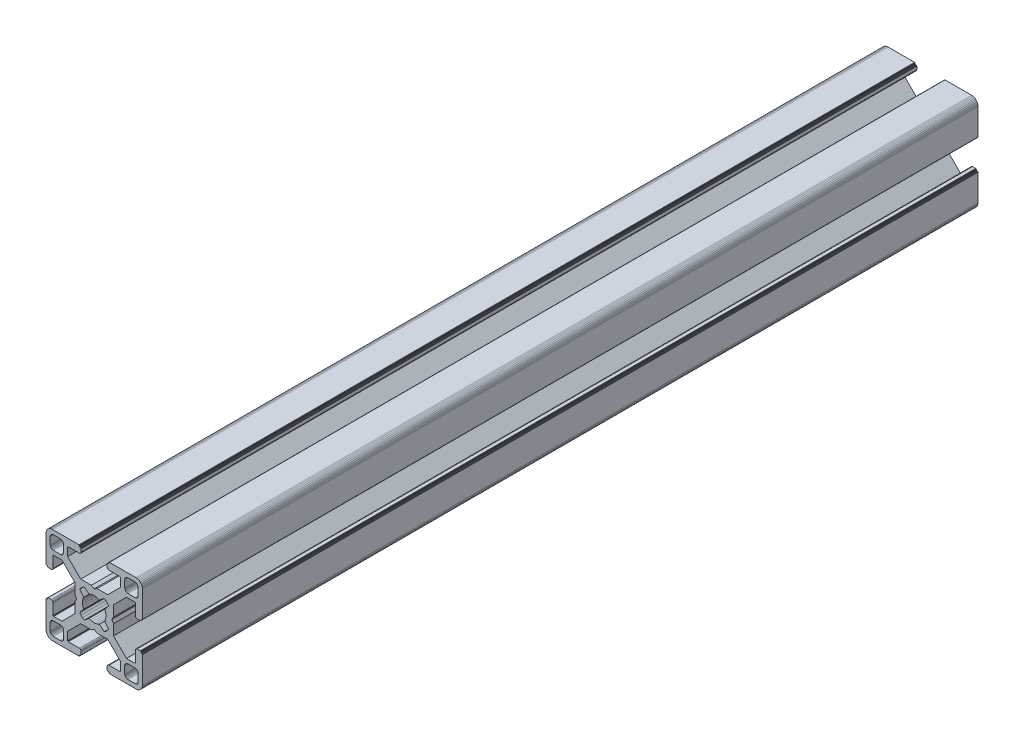
SolidWorks part; units mm, degrees
ref_plane "Front Plane" through (0, 0, 0) normal (0, 0, 1) x (1, 0, 0)
ref_plane "Top Plane" through (0, 0, 0) normal (0, 1, 0) x (1, 0, 0)
ref_plane "Right Plane" through (0, 0, 0) normal (1, 0, 0) x (0, 0, -1)
ref_plane "Plane1" through (0, 0, 0) normal (0, 0, 1) x (1, 0, 0)
sketch "Sketch1" plane through (0, 0, 0) normal (0, 0, 1) x (1, 0, 0)
  line L0 (28.3473, 29.9696) -> (28, 30)
  line L1 (28, 30) -> (19.75, 30)
  line L2 (19.75, 30) -> (19.7153, 29.997)
  line L3 (19.7153, 29.997) -> (19.6816, 29.9879)
  line L4 (19.6816, 29.9879) -> (19.65, 29.9732)
  line L5 (19.65, 29.9732) -> (19.6214, 29.9532)
  line L6 (19.6214, 29.9532) -> (19.5968, 29.9286)
  line L7 (19.5968, 29.9286) -> (19.5768, 29.9)
  line L8 (19.5768, 29.9) -> (19.5621, 29.8684)
  line L9 (19.5621, 29.8684) -> (19.553, 29.8347)
  line L10 (19.553, 29.8347) -> (19.55, 29.8)
  line L11 (19.55, 29.8) -> (19.55, 29.7)
  line L12 (19.55, 29.7) -> (19.547, 29.6653)
  line L13 (19.547, 29.6653) -> (19.5379, 29.6316)
  line L14 (19.5379, 29.6316) -> (19.5232, 29.6)
  line L15 (19.5232, 29.6) -> (19.5032, 29.5714)
  line L16 (19.5032, 29.5714) -> (19.4786, 29.5468)
  line L17 (19.4786, 29.5468) -> (19.45, 29.5268)
  line L18 (19.45, 29.5268) -> (19.4184, 29.5121)
  line L19 (19.4184, 29.5121) -> (19.3847, 29.503)
  line L20 (19.3847, 29.503) -> (19.35, 29.5)
  line L21 (19.35, 29.5) -> (19.25, 29.5)
  line L22 (19.25, 29.5) -> (19.2153, 29.497)
  line L23 (19.2153, 29.497) -> (19.1816, 29.4879)
  line L24 (19.1816, 29.4879) -> (19.15, 29.4732)
  line L25 (19.15, 29.4732) -> (19.1214, 29.4532)
  line L26 (19.1214, 29.4532) -> (19.0968, 29.4286)
  line L27 (19.0968, 29.4286) -> (19.0768, 29.4)
  line L28 (19.0768, 29.4) -> (19.0621, 29.3684)
  line L29 (19.0621, 29.3684) -> (19.053, 29.3347)
  line L30 (19.053, 29.3347) -> (19.05, 29.3)
  line L31 (19.05, 29.3) -> (19.05, 28.4)
  line L32 (19.05, 28.4) -> (19.0591, 28.2958)
  line L33 (19.0591, 28.2958) -> (19.0862, 28.1948)
  line L34 (19.0862, 28.1948) -> (19.1304, 28.1)
  line L35 (19.1304, 28.1) -> (19.1904, 28.0143)
  line L36 (19.1904, 28.0143) -> (19.2643, 27.9404)
  line L37 (19.2643, 27.9404) -> (19.35, 27.8804)
  line L38 (19.35, 27.8804) -> (19.4448, 27.8362)
  line L39 (19.4448, 27.8362) -> (19.5458, 27.8091)
  line L40 (19.5458, 27.8091) -> (19.65, 27.8)
  line L41 (19.65, 27.8) -> (23.05, 27.8)
  line L42 (23.05, 27.8) -> (23.0847, 27.7969)
  line L43 (23.0847, 27.7969) -> (23.1184, 27.7879)
  line L44 (23.1184, 27.7879) -> (23.15, 27.7732)
  line L45 (23.15, 27.7732) -> (23.1786, 27.7532)
  line L46 (23.1786, 27.7532) -> (23.2032, 27.7285)
  line L47 (23.2032, 27.7285) -> (23.2232, 27.7)
  line L48 (23.2232, 27.7) -> (23.2379, 27.6684)
  line L49 (23.2379, 27.6684) -> (23.247, 27.6347)
  line L50 (23.247, 27.6347) -> (23.25, 27.6)
  line L51 (23.25, 27.6) -> (23.25, 25.05)
  line L52 (23.25, 25.05) -> (19.2045, 21)
  line L53 (19.2045, 21) -> (15.9, 21)
  line L54 (15.9, 21) -> (15, 20.4848)
  line L55 (15, 20.4848) -> (14.1, 21)
  line L56 (14.1, 21) -> (10.7955, 21)
  line L57 (10.7955, 21) -> (7.9973, 23.8013)
  line L58 (7.9973, 23.8013) -> (6.75, 25.05)
  line L59 (6.75, 25.05) -> (6.75, 27.6)
  line L60 (6.75, 27.6) -> (6.753, 27.6347)
  line L61 (6.753, 27.6347) -> (6.7621, 27.6684)
  line L62 (6.7621, 27.6684) -> (6.7768, 27.7)
  line L63 (6.7768, 27.7) -> (6.7968, 27.7285)
  line L64 (6.7968, 27.7285) -> (6.8215, 27.7532)
  line L65 (6.8215, 27.7532) -> (6.85, 27.7732)
  line L66 (6.85, 27.7732) -> (6.8816, 27.7879)
  line L67 (6.8816, 27.7879) -> (6.9153, 27.7969)
  line L68 (6.9153, 27.7969) -> (6.95, 27.8)
  line L69 (6.95, 27.8) -> (10.35, 27.8)
  line L70 (10.35, 27.8) -> (10.4542, 27.8091)
  line L71 (10.4542, 27.8091) -> (10.5552, 27.8362)
  line L72 (10.5552, 27.8362) -> (10.65, 27.8804)
  line L73 (10.65, 27.8804) -> (10.7357, 27.9404)
  line L74 (10.7357, 27.9404) -> (10.8096, 28.0143)
  line L75 (10.8096, 28.0143) -> (10.8696, 28.1)
  line L76 (10.8696, 28.1) -> (10.9138, 28.1948)
  line L77 (10.9138, 28.1948) -> (10.9409, 28.2958)
  line L78 (10.9409, 28.2958) -> (10.95, 28.4)
  line L79 (10.95, 28.4) -> (10.95, 29.3)
  line L80 (10.95, 29.3) -> (10.947, 29.3347)
  line L81 (10.947, 29.3347) -> (10.938, 29.3684)
  line L82 (10.938, 29.3684) -> (10.9232, 29.4)
  line L83 (10.9232, 29.4) -> (10.9032, 29.4286)
  line L84 (10.9032, 29.4286) -> (10.8786, 29.4532)
  line L85 (10.8786, 29.4532) -> (10.85, 29.4732)
  line L86 (10.85, 29.4732) -> (10.8184, 29.4879)
  line L87 (10.8184, 29.4879) -> (10.7847, 29.497)
  line L88 (10.7847, 29.497) -> (10.75, 29.5)
  line L89 (10.75, 29.5) -> (10.65, 29.5)
  line L90 (10.65, 29.5) -> (10.6153, 29.503)
  line L91 (10.6153, 29.503) -> (10.5816, 29.5121)
  line L92 (10.5816, 29.5121) -> (10.55, 29.5268)
  line L93 (10.55, 29.5268) -> (10.5214, 29.5468)
  line L94 (10.5214, 29.5468) -> (10.4968, 29.5714)
  line L95 (10.4968, 29.5714) -> (10.4768, 29.6)
  line L96 (10.4768, 29.6) -> (10.4621, 29.6316)
  line L97 (10.4621, 29.6316) -> (10.453, 29.6653)
  line L98 (10.453, 29.6653) -> (10.45, 29.7)
  line L99 (10.45, 29.7) -> (10.45, 29.8)
  line L100 (10.45, 29.8) -> (10.447, 29.8347)
  line L101 (10.447, 29.8347) -> (10.4379, 29.8684)
  line L102 (10.4379, 29.8684) -> (10.4232, 29.9)
  line L103 (10.4232, 29.9) -> (10.4032, 29.9286)
  line L104 (10.4032, 29.9286) -> (10.3786, 29.9532)
  line L105 (10.3786, 29.9532) -> (10.35, 29.9732)
  line L106 (10.35, 29.9732) -> (10.3184, 29.9879)
  line L107 (10.3184, 29.9879) -> (10.2847, 29.997)
  line L108 (10.2847, 29.997) -> (10.25, 30)
  line L109 (10.25, 30) -> (2, 30)
  line L110 (2, 30) -> (1.6527, 29.9696)
  line L111 (1.6527, 29.9696) -> (1.316, 29.8794)
  line L112 (1.316, 29.8794) -> (1, 29.7321)
  line L113 (1, 29.7321) -> (0.7144, 29.5321)
  line L114 (0.7144, 29.5321) -> (0.4679, 29.2856)
  line L115 (0.4679, 29.2856) -> (0.2679, 29)
  line L116 (0.2679, 29) -> (0.1206, 28.684)
  line L117 (0.1206, 28.684) -> (0.0304, 28.3473)
  line L118 (0.0304, 28.3473) -> (0, 28)
  line L119 (0, 28) -> (0, 19.75)
  line L120 (0, 19.75) -> (0.003, 19.7153)
  line L121 (0.003, 19.7153) -> (0.0121, 19.6816)
  line L122 (0.0121, 19.6816) -> (0.0268, 19.65)
  line L123 (0.0268, 19.65) -> (0.0468, 19.6214)
  line L124 (0.0468, 19.6214) -> (0.0714, 19.5968)
  line L125 (0.0714, 19.5968) -> (0.1, 19.5768)
  line L126 (0.1, 19.5768) -> (0.1316, 19.5621)
  line L127 (0.1316, 19.5621) -> (0.1653, 19.553)
  line L128 (0.1653, 19.553) -> (0.2, 19.55)
  line L129 (0.2, 19.55) -> (0.3, 19.55)
  line L130 (0.3, 19.55) -> (0.3347, 19.547)
  line L131 (0.3347, 19.547) -> (0.3684, 19.5379)
  line L132 (0.3684, 19.5379) -> (0.4, 19.5232)
  line L133 (0.4, 19.5232) -> (0.4286, 19.5032)
  line L134 (0.4286, 19.5032) -> (0.4532, 19.4786)
  line L135 (0.4532, 19.4786) -> (0.4732, 19.45)
  line L136 (0.4732, 19.45) -> (0.4879, 19.4184)
  line L137 (0.4879, 19.4184) -> (0.497, 19.3847)
  line L138 (0.497, 19.3847) -> (0.5, 19.35)
  line L139 (0.5, 19.35) -> (0.5, 19.25)
  line L140 (0.5, 19.25) -> (0.503, 19.2153)
  line L141 (0.503, 19.2153) -> (0.5121, 19.1816)
  line L142 (0.5121, 19.1816) -> (0.5268, 19.15)
  line L143 (0.5268, 19.15) -> (0.5468, 19.1214)
  line L144 (0.5468, 19.1214) -> (0.5714, 19.0968)
  line L145 (0.5714, 19.0968) -> (0.6, 19.0768)
  line L146 (0.6, 19.0768) -> (0.6316, 19.0621)
  line L147 (0.6316, 19.0621) -> (0.6653, 19.053)
  line L148 (0.6653, 19.053) -> (0.7, 19.05)
  line L149 (0.7, 19.05) -> (1.6, 19.05)
  line L150 (1.6, 19.05) -> (1.7042, 19.0591)
  line L151 (1.7042, 19.0591) -> (1.8052, 19.0862)
  line L152 (1.8052, 19.0862) -> (1.9, 19.1304)
  line L153 (1.9, 19.1304) -> (1.9857, 19.1904)
  line L154 (1.9857, 19.1904) -> (2.0596, 19.2643)
  line L155 (2.0596, 19.2643) -> (2.1196, 19.35)
  line L156 (2.1196, 19.35) -> (2.1638, 19.4448)
  line L157 (2.1638, 19.4448) -> (2.1909, 19.5458)
  line L158 (2.1909, 19.5458) -> (2.2, 19.65)
  line L159 (2.2, 19.65) -> (2.2, 23.05)
  line L160 (2.2, 23.05) -> (2.203, 23.0847)
  line L161 (2.203, 23.0847) -> (2.2121, 23.1184)
  line L162 (2.2121, 23.1184) -> (2.2268, 23.15)
  line L163 (2.2268, 23.15) -> (2.2468, 23.1786)
  line L164 (2.2468, 23.1786) -> (2.2714, 23.2032)
  line L165 (2.2714, 23.2032) -> (2.3, 23.2232)
  line L166 (2.3, 23.2232) -> (2.3316, 23.2379)
  line L167 (2.3316, 23.2379) -> (2.3653, 23.247)
  line L168 (2.3653, 23.247) -> (2.4, 23.25)
  line L169 (2.4, 23.25) -> (4.95, 23.25)
  line L170 (4.95, 23.25) -> (7.9973, 20.2027)
  line L171 (7.9973, 20.2027) -> (8.9955, 19.2045)
  line L172 (8.9955, 19.2045) -> (8.9955, 15.9)
  line L173 (8.9955, 15.9) -> (9.5151, 15)
  line L174 (9.5151, 15) -> (8.9955, 14.1)
  line L175 (8.9955, 14.1) -> (8.9955, 10.7955)
  line L176 (8.9955, 10.7955) -> (4.95, 6.75)
  line L177 (4.95, 6.75) -> (2.4, 6.75)
  line L178 (2.4, 6.75) -> (2.3653, 6.753)
  line L179 (2.3653, 6.753) -> (2.3316, 6.7621)
  line L180 (2.3316, 6.7621) -> (2.3, 6.7768)
  line L181 (2.3, 6.7768) -> (2.2714, 6.7968)
  line L182 (2.2714, 6.7968) -> (2.2468, 6.8214)
  line L183 (2.2468, 6.8214) -> (2.2268, 6.85)
  line L184 (2.2268, 6.85) -> (2.2121, 6.8816)
  line L185 (2.2121, 6.8816) -> (2.203, 6.9153)
  line L186 (2.203, 6.9153) -> (2.2, 6.95)
  line L187 (2.2, 6.95) -> (2.2, 10.35)
  line L188 (2.2, 10.35) -> (2.1909, 10.4542)
  line L189 (2.1909, 10.4542) -> (2.1638, 10.5552)
  line L190 (2.1638, 10.5552) -> (2.1196, 10.65)
  line L191 (2.1196, 10.65) -> (2.0596, 10.7357)
  line L192 (2.0596, 10.7357) -> (1.9857, 10.8096)
  line L193 (1.9857, 10.8096) -> (1.9, 10.8696)
  line L194 (1.9, 10.8696) -> (1.8052, 10.9138)
  line L195 (1.8052, 10.9138) -> (1.7042, 10.9409)
  line L196 (1.7042, 10.9409) -> (1.6, 10.95)
  line L197 (1.6, 10.95) -> (0.7, 10.95)
  line L198 (0.7, 10.95) -> (0.6653, 10.9469)
  line L199 (0.6653, 10.9469) -> (0.6316, 10.9379)
  line L200 (0.6316, 10.9379) -> (0.6, 10.9232)
  line L201 (0.6, 10.9232) -> (0.5715, 10.9032)
  line L202 (0.5715, 10.9032) -> (0.5468, 10.8785)
  line L203 (0.5468, 10.8785) -> (0.5268, 10.85)
  line L204 (0.5268, 10.85) -> (0.5121, 10.8184)
  line L205 (0.5121, 10.8184) -> (0.503, 10.7847)
  line L206 (0.503, 10.7847) -> (0.5, 10.75)
  line L207 (0.5, 10.75) -> (0.5, 10.65)
  line L208 (0.5, 10.65) -> (0.497, 10.6153)
  line L209 (0.497, 10.6153) -> (0.4879, 10.5816)
  line L210 (0.4879, 10.5816) -> (0.4732, 10.55)
  line L211 (0.4732, 10.55) -> (0.4532, 10.5214)
  line L212 (0.4532, 10.5214) -> (0.4286, 10.4968)
  line L213 (0.4286, 10.4968) -> (0.4, 10.4768)
  line L214 (0.4, 10.4768) -> (0.3684, 10.4621)
  line L215 (0.3684, 10.4621) -> (0.3347, 10.453)
  line L216 (0.3347, 10.453) -> (0.3, 10.45)
  line L217 (0.3, 10.45) -> (0.2, 10.45)
  line L218 (0.2, 10.45) -> (0.1653, 10.447)
  line L219 (0.1653, 10.447) -> (0.1316, 10.4379)
  line L220 (0.1316, 10.4379) -> (0.1, 10.4232)
  line L221 (0.1, 10.4232) -> (0.0714, 10.4032)
  line L222 (0.0714, 10.4032) -> (0.0468, 10.3786)
  line L223 (0.0468, 10.3786) -> (0.0268, 10.35)
  line L224 (0.0268, 10.35) -> (0.0121, 10.3184)
  line L225 (0.0121, 10.3184) -> (0.003, 10.2847)
  line L226 (0.003, 10.2847) -> (0, 10.25)
  line L227 (0, 10.25) -> (0, 2)
  line L228 (0, 2) -> (0.0304, 1.6527)
  line L229 (0.0304, 1.6527) -> (0.1206, 1.316)
  line L230 (0.1206, 1.316) -> (0.2679, 1)
  line L231 (0.2679, 1) -> (0.4679, 0.7144)
  line L232 (0.4679, 0.7144) -> (0.7144, 0.4679)
  line L233 (0.7144, 0.4679) -> (1, 0.2679)
  line L234 (1, 0.2679) -> (1.316, 0.1206)
  line L235 (1.316, 0.1206) -> (1.6527, 0.0304)
  line L236 (1.6527, 0.0304) -> (2, 0)
  line L237 (2, 0) -> (10.25, 0)
  line L238 (10.25, 0) -> (10.2847, 0.003)
  line L239 (10.2847, 0.003) -> (10.3184, 0.0121)
  line L240 (10.3184, 0.0121) -> (10.35, 0.0268)
  line L241 (10.35, 0.0268) -> (10.3786, 0.0468)
  line L242 (10.3786, 0.0468) -> (10.4032, 0.0714)
  line L243 (10.4032, 0.0714) -> (10.4232, 0.1)
  line L244 (10.4232, 0.1) -> (10.4379, 0.1316)
  line L245 (10.4379, 0.1316) -> (10.447, 0.1653)
  line L246 (10.447, 0.1653) -> (10.45, 0.2)
  line L247 (10.45, 0.2) -> (10.45, 0.3)
  line L248 (10.45, 0.3) -> (10.453, 0.3347)
  line L249 (10.453, 0.3347) -> (10.4621, 0.3684)
  line L250 (10.4621, 0.3684) -> (10.4768, 0.4)
  line L251 (10.4768, 0.4) -> (10.4968, 0.4286)
  line L252 (10.4968, 0.4286) -> (10.5214, 0.4532)
  line L253 (10.5214, 0.4532) -> (10.55, 0.4732)
  line L254 (10.55, 0.4732) -> (10.5816, 0.4879)
  line L255 (10.5816, 0.4879) -> (10.6153, 0.497)
  line L256 (10.6153, 0.497) -> (10.65, 0.5)
  line L257 (10.65, 0.5) -> (10.75, 0.5)
  line L258 (10.75, 0.5) -> (10.7847, 0.503)
  line L259 (10.7847, 0.503) -> (10.8184, 0.5121)
  line L260 (10.8184, 0.5121) -> (10.85, 0.5268)
  line L261 (10.85, 0.5268) -> (10.8785, 0.5468)
  line L262 (10.8785, 0.5468) -> (10.9032, 0.5715)
  line L263 (10.9032, 0.5715) -> (10.9232, 0.6)
  line L264 (10.9232, 0.6) -> (10.9379, 0.6316)
  line L265 (10.9379, 0.6316) -> (10.9469, 0.6653)
  line L266 (10.9469, 0.6653) -> (10.95, 0.7)
  line L267 (10.95, 0.7) -> (10.95, 1.6)
  line L268 (10.95, 1.6) -> (10.9409, 1.7042)
  line L269 (10.9409, 1.7042) -> (10.9138, 1.8052)
  line L270 (10.9138, 1.8052) -> (10.8696, 1.9)
  line L271 (10.8696, 1.9) -> (10.8096, 1.9857)
  line L272 (10.8096, 1.9857) -> (10.7357, 2.0596)
  line L273 (10.7357, 2.0596) -> (10.65, 2.1196)
  line L274 (10.65, 2.1196) -> (10.5552, 2.1638)
  line L275 (10.5552, 2.1638) -> (10.4542, 2.1909)
  line L276 (10.4542, 2.1909) -> (10.35, 2.2)
  line L277 (10.35, 2.2) -> (6.95, 2.2)
  line L278 (6.95, 2.2) -> (6.9153, 2.203)
  line L279 (6.9153, 2.203) -> (6.8816, 2.212)
  line L280 (6.8816, 2.212) -> (6.85, 2.2268)
  line L281 (6.85, 2.2268) -> (6.8215, 2.2468)
  line L282 (6.8215, 2.2468) -> (6.7968, 2.2714)
  line L283 (6.7968, 2.2714) -> (6.7768, 2.3)
  line L284 (6.7768, 2.3) -> (6.7621, 2.3316)
  line L285 (6.7621, 2.3316) -> (6.753, 2.3653)
  line L286 (6.753, 2.3653) -> (6.75, 2.4)
  line L287 (6.75, 2.4) -> (6.75, 4.95)
  line L288 (6.75, 4.95) -> (9.7875, 7.9908)
  line L289 (9.7875, 7.9908) -> (10.7955, 9)
  line L290 (10.7955, 9) -> (14.1, 9)
  line L291 (14.1, 9) -> (15, 9.5151)
  line L292 (15, 9.5151) -> (15.9, 9)
  line L293 (15.9, 9) -> (19.2045, 9)
  line L294 (19.2045, 9) -> (20.2126, 7.9908)
  line L295 (20.2126, 7.9908) -> (23.25, 4.95)
  line L296 (23.25, 4.95) -> (23.25, 2.4)
  line L297 (23.25, 2.4) -> (23.247, 2.3653)
  line L298 (23.247, 2.3653) -> (23.2379, 2.3316)
  line L299 (23.2379, 2.3316) -> (23.2232, 2.3)
  line L300 (23.2232, 2.3) -> (23.2032, 2.2714)
  line L301 (23.2032, 2.2714) -> (23.1786, 2.2468)
  line L302 (23.1786, 2.2468) -> (23.15, 2.2268)
  line L303 (23.15, 2.2268) -> (23.1184, 2.212)
  line L304 (23.1184, 2.212) -> (23.0847, 2.203)
  line L305 (23.0847, 2.203) -> (23.05, 2.2)
  line L306 (23.05, 2.2) -> (19.65, 2.2)
  line L307 (19.65, 2.2) -> (19.5458, 2.1909)
  line L308 (19.5458, 2.1909) -> (19.4448, 2.1638)
  line L309 (19.4448, 2.1638) -> (19.35, 2.1196)
  line L310 (19.35, 2.1196) -> (19.2643, 2.0596)
  line L311 (19.2643, 2.0596) -> (19.1904, 1.9857)
  line L312 (19.1904, 1.9857) -> (19.1304, 1.9)
  line L313 (19.1304, 1.9) -> (19.0862, 1.8052)
  line L314 (19.0862, 1.8052) -> (19.0591, 1.7042)
  line L315 (19.0591, 1.7042) -> (19.05, 1.6)
  line L316 (19.05, 1.6) -> (19.05, 0.7)
  line L317 (19.05, 0.7) -> (19.053, 0.6653)
  line L318 (19.053, 0.6653) -> (19.0621, 0.6316)
  line L319 (19.0621, 0.6316) -> (19.0768, 0.6)
  line L320 (19.0768, 0.6) -> (19.0968, 0.5714)
  line L321 (19.0968, 0.5714) -> (19.1214, 0.5468)
  line L322 (19.1214, 0.5468) -> (19.15, 0.5268)
  line L323 (19.15, 0.5268) -> (19.1816, 0.5121)
  line L324 (19.1816, 0.5121) -> (19.2153, 0.503)
  line L325 (19.2153, 0.503) -> (19.25, 0.5)
  line L326 (19.25, 0.5) -> (19.35, 0.5)
  line L327 (19.35, 0.5) -> (19.3847, 0.497)
  line L328 (19.3847, 0.497) -> (19.4184, 0.4879)
  line L329 (19.4184, 0.4879) -> (19.45, 0.4732)
  line L330 (19.45, 0.4732) -> (19.4786, 0.4532)
  line L331 (19.4786, 0.4532) -> (19.5032, 0.4286)
  line L332 (19.5032, 0.4286) -> (19.5232, 0.4)
  line L333 (19.5232, 0.4) -> (19.5379, 0.3684)
  line L334 (19.5379, 0.3684) -> (19.547, 0.3347)
  line L335 (19.547, 0.3347) -> (19.55, 0.3)
  line L336 (19.55, 0.3) -> (19.55, 0.2)
  line L337 (19.55, 0.2) -> (19.553, 0.1653)
  line L338 (19.553, 0.1653) -> (19.5621, 0.1316)
  line L339 (19.5621, 0.1316) -> (19.5768, 0.1)
  line L340 (19.5768, 0.1) -> (19.5968, 0.0714)
  line L341 (19.5968, 0.0714) -> (19.6214, 0.0468)
  line L342 (19.6214, 0.0468) -> (19.65, 0.0268)
  line L343 (19.65, 0.0268) -> (19.6816, 0.0121)
  line L344 (19.6816, 0.0121) -> (19.7153, 0.003)
  line L345 (19.7153, 0.003) -> (19.75, 0)
  line L346 (19.75, 0) -> (28, 0)
  line L347 (28, 0) -> (28.3473, 0.0304)
  line L348 (28.3473, 0.0304) -> (28.684, 0.1206)
  line L349 (28.684, 0.1206) -> (29, 0.2679)
  line L350 (29, 0.2679) -> (29.2856, 0.4679)
  line L351 (29.2856, 0.4679) -> (29.5321, 0.7144)
  line L352 (29.5321, 0.7144) -> (29.7321, 1)
  line L353 (29.7321, 1) -> (29.8794, 1.316)
  line L354 (29.8794, 1.316) -> (29.9696, 1.6527)
  line L355 (29.9696, 1.6527) -> (30, 2)
  line L356 (30, 2) -> (30, 10.25)
  line L357 (30, 10.25) -> (29.997, 10.2847)
  line L358 (29.997, 10.2847) -> (29.988, 10.3184)
  line L359 (29.988, 10.3184) -> (29.9732, 10.35)
  line L360 (29.9732, 10.35) -> (29.9532, 10.3785)
  line L361 (29.9532, 10.3785) -> (29.9286, 10.4032)
  line L362 (29.9286, 10.4032) -> (29.9, 10.4232)
  line L363 (29.9, 10.4232) -> (29.8684, 10.4379)
  line L364 (29.8684, 10.4379) -> (29.8347, 10.447)
  line L365 (29.8347, 10.447) -> (29.8, 10.45)
  line L366 (29.8, 10.45) -> (29.7, 10.45)
  line L367 (29.7, 10.45) -> (29.6649, 10.4534)
  line L368 (29.6649, 10.4534) -> (29.6312, 10.4624)
  line L369 (29.6312, 10.4624) -> (29.5996, 10.4772)
  line L370 (29.5996, 10.4772) -> (29.5711, 10.4972)
  line L371 (29.5711, 10.4972) -> (29.5464, 10.5218)
  line L372 (29.5464, 10.5218) -> (29.5264, 10.5504)
  line L373 (29.5264, 10.5504) -> (29.5117, 10.582)
  line L374 (29.5117, 10.582) -> (29.5027, 10.6156)
  line L375 (29.5027, 10.6156) -> (29.4996, 10.6504)
  line L376 (29.4996, 10.6504) -> (29.4996, 10.7504)
  line L377 (29.4996, 10.7504) -> (29.497, 10.7847)
  line L378 (29.497, 10.7847) -> (29.4879, 10.8184)
  line L379 (29.4879, 10.8184) -> (29.4732, 10.85)
  line L380 (29.4732, 10.85) -> (29.4532, 10.8785)
  line L381 (29.4532, 10.8785) -> (29.4286, 10.9032)
  line L382 (29.4286, 10.9032) -> (29.4, 10.9232)
  line L383 (29.4, 10.9232) -> (29.3684, 10.9379)
  line L384 (29.3684, 10.9379) -> (29.3347, 10.9469)
  line L385 (29.3347, 10.9469) -> (29.3, 10.95)
  line L386 (29.3, 10.95) -> (28.4, 10.95)
  line L387 (28.4, 10.95) -> (28.2958, 10.9409)
  line L388 (28.2958, 10.9409) -> (28.1948, 10.9138)
  line L389 (28.1948, 10.9138) -> (28.1, 10.8696)
  line L390 (28.1, 10.8696) -> (28.0143, 10.8096)
  line L391 (28.0143, 10.8096) -> (27.9404, 10.7357)
  line L392 (27.9404, 10.7357) -> (27.8804, 10.65)
  line L393 (27.8804, 10.65) -> (27.8362, 10.5552)
  line L394 (27.8362, 10.5552) -> (27.8091, 10.4542)
  line L395 (27.8091, 10.4542) -> (27.8, 10.35)
  line L396 (27.8, 10.35) -> (27.8, 6.95)
  line L397 (27.8, 6.95) -> (27.797, 6.9153)
  line L398 (27.797, 6.9153) -> (27.7879, 6.8816)
  line L399 (27.7879, 6.8816) -> (27.7732, 6.85)
  line L400 (27.7732, 6.85) -> (27.7532, 6.8214)
  line L401 (27.7532, 6.8214) -> (27.7286, 6.7968)
  line L402 (27.7286, 6.7968) -> (27.7, 6.7768)
  line L403 (27.7, 6.7768) -> (27.6684, 6.7621)
  line L404 (27.6684, 6.7621) -> (27.6347, 6.753)
  line L405 (27.6347, 6.753) -> (27.6, 6.75)
  line L406 (27.6, 6.75) -> (25.05, 6.75)
  line L407 (25.05, 6.75) -> (23.8092, 7.9908)
  line L408 (23.8092, 7.9908) -> (21.0045, 10.7955)
  line L409 (21.0045, 10.7955) -> (21.0045, 14.1)
  line L410 (21.0045, 14.1) -> (20.4849, 15)
  line L411 (20.4849, 15) -> (21.0045, 15.9)
  line L412 (21.0045, 15.9) -> (21.0045, 19.2045)
  line L413 (21.0045, 19.2045) -> (25.05, 23.25)
  line L414 (25.05, 23.25) -> (27.6, 23.25)
  line L415 (27.6, 23.25) -> (27.6347, 23.247)
  line L416 (27.6347, 23.247) -> (27.6684, 23.2379)
  line L417 (27.6684, 23.2379) -> (27.7, 23.2232)
  line L418 (27.7, 23.2232) -> (27.7286, 23.2032)
  line L419 (27.7286, 23.2032) -> (27.7532, 23.1786)
  line L420 (27.7532, 23.1786) -> (27.7732, 23.15)
  line L421 (27.7732, 23.15) -> (27.7879, 23.1184)
  line L422 (27.7879, 23.1184) -> (27.797, 23.0847)
  line L423 (27.797, 23.0847) -> (27.8, 23.05)
  line L424 (27.8, 23.05) -> (27.8, 19.65)
  line L425 (27.8, 19.65) -> (27.8091, 19.5458)
  line L426 (27.8091, 19.5458) -> (27.8362, 19.4448)
  line L427 (27.8362, 19.4448) -> (27.8804, 19.35)
  line L428 (27.8804, 19.35) -> (27.9404, 19.2643)
  line L429 (27.9404, 19.2643) -> (28.0143, 19.1904)
  line L430 (28.0143, 19.1904) -> (28.1, 19.1304)
  line L431 (28.1, 19.1304) -> (28.1948, 19.0862)
  line L432 (28.1948, 19.0862) -> (28.2958, 19.0591)
  line L433 (28.2958, 19.0591) -> (28.4, 19.05)
  line L434 (28.4, 19.05) -> (29.3, 19.05)
  line L435 (29.3, 19.05) -> (29.3347, 19.053)
  line L436 (29.3347, 19.053) -> (29.3684, 19.0621)
  line L437 (29.3684, 19.0621) -> (29.4, 19.0768)
  line L438 (29.4, 19.0768) -> (29.4282, 19.0971)
  line L439 (29.4282, 19.0971) -> (29.4528, 19.1218)
  line L440 (29.4528, 19.1218) -> (29.4728, 19.1504)
  line L441 (29.4728, 19.1504) -> (29.4876, 19.182)
  line L442 (29.4876, 19.182) -> (29.4966, 19.2156)
  line L443 (29.4966, 19.2156) -> (29.4996, 19.2504)
  line L444 (29.4996, 19.2504) -> (29.4996, 19.3504)
  line L445 (29.4996, 19.3504) -> (29.5027, 19.3851)
  line L446 (29.5027, 19.3851) -> (29.5117, 19.4188)
  line L447 (29.5117, 19.4188) -> (29.5264, 19.4504)
  line L448 (29.5264, 19.4504) -> (29.5464, 19.4789)
  line L449 (29.5464, 19.4789) -> (29.5711, 19.5036)
  line L450 (29.5711, 19.5036) -> (29.5996, 19.5236)
  line L451 (29.5996, 19.5236) -> (29.6312, 19.5383)
  line L452 (29.6312, 19.5383) -> (29.6649, 19.5473)
  line L453 (29.6649, 19.5473) -> (29.7, 19.55)
  line L454 (29.7, 19.55) -> (29.8, 19.55)
  line L455 (29.8, 19.55) -> (29.8347, 19.553)
  line L456 (29.8347, 19.553) -> (29.8684, 19.5621)
  line L457 (29.8684, 19.5621) -> (29.9, 19.5768)
  line L458 (29.9, 19.5768) -> (29.9286, 19.5968)
  line L459 (29.9286, 19.5968) -> (29.9532, 19.6214)
  line L460 (29.9532, 19.6214) -> (29.9732, 19.65)
  line L461 (29.9732, 19.65) -> (29.9879, 19.6816)
  line L462 (29.9879, 19.6816) -> (29.997, 19.7153)
  line L463 (29.997, 19.7153) -> (30, 19.75)
  line L464 (30, 19.75) -> (30, 28)
  line L465 (30, 28) -> (29.9696, 28.3473)
  line L466 (29.9696, 28.3473) -> (29.8794, 28.684)
  line L467 (29.8794, 28.684) -> (29.7321, 29)
  line L468 (29.7321, 29) -> (29.5321, 29.2856)
  line L469 (29.5321, 29.2856) -> (29.2856, 29.5321)
  line L470 (29.2856, 29.5321) -> (29, 29.7321)
  line L471 (29, 29.7321) -> (28.684, 29.8794)
  line L472 (28.684, 29.8794) -> (28.3473, 29.9696)
  line L473 (1.3, 25.5) -> (1.3, 27.7)
  line L474 (1.3, 27.7) -> (1.3123, 27.8564)
  line L475 (1.3123, 27.8564) -> (1.3489, 28.009)
  line L476 (1.3489, 28.009) -> (1.409, 28.154)
  line L477 (1.409, 28.154) -> (1.491, 28.2878)
  line L478 (1.491, 28.2878) -> (1.5929, 28.4071)
  line L479 (1.5929, 28.4071) -> (1.7122, 28.509)
  line L480 (1.7122, 28.509) -> (1.846, 28.591)
  line L481 (1.846, 28.591) -> (1.991, 28.6511)
  line L482 (1.991, 28.6511) -> (2.1436, 28.6877)
  line L483 (2.1436, 28.6877) -> (2.3, 28.7)
  line L484 (2.3, 28.7) -> (4.5, 28.7)
  line L485 (4.5, 28.7) -> (4.6564, 28.6877)
  line L486 (4.6564, 28.6877) -> (4.809, 28.6511)
  line L487 (4.809, 28.6511) -> (4.954, 28.591)
  line L488 (4.954, 28.591) -> (5.0878, 28.509)
  line L489 (5.0878, 28.509) -> (5.2071, 28.4071)
  line L490 (5.2071, 28.4071) -> (5.309, 28.2878)
  line L491 (5.309, 28.2878) -> (5.391, 28.154)
  line L492 (5.391, 28.154) -> (5.4511, 28.009)
  line L493 (5.4511, 28.009) -> (5.4877, 27.8564)
  line L494 (5.4877, 27.8564) -> (5.5, 27.7)
  line L495 (5.5, 27.7) -> (5.5, 25.5)
  line L496 (5.5, 25.5) -> (5.4877, 25.3436)
  line L497 (5.4877, 25.3436) -> (5.4511, 25.191)
  line L498 (5.4511, 25.191) -> (5.391, 25.046)
  line L499 (5.391, 25.046) -> (5.309, 24.9122)
  line L500 (5.309, 24.9122) -> (5.2071, 24.7929)
  line L501 (5.2071, 24.7929) -> (5.0878, 24.691)
  line L502 (5.0878, 24.691) -> (4.954, 24.609)
  line L503 (4.954, 24.609) -> (4.809, 24.5489)
  line L504 (4.809, 24.5489) -> (4.6564, 24.5123)
  line L505 (4.6564, 24.5123) -> (4.5, 24.5)
  line L506 (4.5, 24.5) -> (2.3, 24.5)
  line L507 (2.3, 24.5) -> (2.1436, 24.5123)
  line L508 (2.1436, 24.5123) -> (1.991, 24.5489)
  line L509 (1.991, 24.5489) -> (1.846, 24.609)
  line L510 (1.846, 24.609) -> (1.7122, 24.691)
  line L511 (1.7122, 24.691) -> (1.5929, 24.7929)
  line L512 (1.5929, 24.7929) -> (1.491, 24.9122)
  line L513 (1.491, 24.9122) -> (1.409, 25.046)
  line L514 (1.409, 25.046) -> (1.3489, 25.191)
  line L515 (1.3489, 25.191) -> (1.3123, 25.3436)
  line L516 (1.3123, 25.3436) -> (1.3, 25.5)
  line L517 (25.3436, 28.6877) -> (25.5, 28.7)
  line L518 (25.5, 28.7) -> (27.7, 28.7)
  line L519 (27.7, 28.7) -> (27.8564, 28.6877)
  line L520 (27.8564, 28.6877) -> (28.009, 28.6511)
  line L521 (28.009, 28.6511) -> (28.154, 28.591)
  line L522 (28.154, 28.591) -> (28.2878, 28.509)
  line L523 (28.2878, 28.509) -> (28.4071, 28.4071)
  line L524 (28.4071, 28.4071) -> (28.509, 28.2878)
  line L525 (28.509, 28.2878) -> (28.591, 28.154)
  line L526 (28.591, 28.154) -> (28.6511, 28.009)
  line L527 (28.6511, 28.009) -> (28.6877, 27.8564)
  line L528 (28.6877, 27.8564) -> (28.7, 27.7)
  line L529 (28.7, 27.7) -> (28.7, 25.5)
  line L530 (28.7, 25.5) -> (28.6877, 25.3436)
  line L531 (28.6877, 25.3436) -> (28.6511, 25.191)
  line L532 (28.6511, 25.191) -> (28.591, 25.046)
  line L533 (28.591, 25.046) -> (28.509, 24.9122)
  line L534 (28.509, 24.9122) -> (28.4071, 24.7929)
  line L535 (28.4071, 24.7929) -> (28.2878, 24.691)
  line L536 (28.2878, 24.691) -> (28.154, 24.609)
  line L537 (28.154, 24.609) -> (28.009, 24.5489)
  line L538 (28.009, 24.5489) -> (27.8564, 24.5123)
  line L539 (27.8564, 24.5123) -> (27.7, 24.5)
  line L540 (27.7, 24.5) -> (25.5, 24.5)
  line L541 (25.5, 24.5) -> (25.3436, 24.5123)
  line L542 (25.3436, 24.5123) -> (25.191, 24.5489)
  line L543 (25.191, 24.5489) -> (25.046, 24.609)
  line L544 (25.046, 24.609) -> (24.9122, 24.691)
  line L545 (24.9122, 24.691) -> (24.7929, 24.7929)
  line L546 (24.7929, 24.7929) -> (24.691, 24.9122)
  line L547 (24.691, 24.9122) -> (24.609, 25.046)
  line L548 (24.609, 25.046) -> (24.5489, 25.191)
  line L549 (24.5489, 25.191) -> (24.5123, 25.3436)
  line L550 (24.5123, 25.3436) -> (24.5, 25.5)
  line L551 (24.5, 25.5) -> (24.5, 27.7)
  line L552 (24.5, 27.7) -> (24.5123, 27.8564)
  line L553 (24.5123, 27.8564) -> (24.5489, 28.009)
  line L554 (24.5489, 28.009) -> (24.609, 28.154)
  line L555 (24.609, 28.154) -> (24.691, 28.2878)
  line L556 (24.691, 28.2878) -> (24.7929, 28.4071)
  line L557 (24.7929, 28.4071) -> (24.9122, 28.509)
  line L558 (24.9122, 28.509) -> (25.046, 28.591)
  line L559 (25.046, 28.591) -> (25.191, 28.6511)
  line L560 (25.191, 28.6511) -> (25.3436, 28.6877)
  line L561 (15, 18.65) -> (15.55, 18.6083)
  line L562 (15.55, 18.6083) -> (16.0875, 18.4842)
  line L563 (16.0875, 18.4842) -> (16.6001, 18.2806)
  line L564 (16.6001, 18.2806) -> (18.1359, 19.5184)
  line L565 (18.1359, 19.5184) -> (18.645, 19.1187)
  line L566 (18.645, 19.1187) -> (19.1036, 18.6621)
  line L567 (19.1036, 18.6621) -> (19.5053, 18.1547)
  line L568 (19.5053, 18.1547) -> (18.2806, 16.6001)
  line L569 (18.2806, 16.6001) -> (18.4842, 16.0875)
  line L570 (18.4842, 16.0875) -> (18.6083, 15.55)
  line L571 (18.6083, 15.55) -> (18.65, 15)
  line L572 (18.65, 15) -> (18.6083, 14.45)
  line L573 (18.6083, 14.45) -> (18.4842, 13.9125)
  line L574 (18.4842, 13.9125) -> (18.2806, 13.3999)
  line L575 (18.2806, 13.3999) -> (19.5053, 11.8453)
  line L576 (19.5053, 11.8453) -> (19.1036, 11.3379)
  line L577 (19.1036, 11.3379) -> (18.645, 10.8813)
  line L578 (18.645, 10.8813) -> (18.1359, 10.4816)
  line L579 (18.1359, 10.4816) -> (16.6001, 11.7194)
  line L580 (16.6001, 11.7194) -> (16.0875, 11.5158)
  line L581 (16.0875, 11.5158) -> (15.55, 11.3917)
  line L582 (15.55, 11.3917) -> (15, 11.35)
  line L583 (15, 11.35) -> (14.45, 11.3917)
  line L584 (14.45, 11.3917) -> (13.9125, 11.5158)
  line L585 (13.9125, 11.5158) -> (13.3999, 11.7194)
  line L586 (13.3999, 11.7194) -> (11.8641, 10.4816)
  line L587 (11.8641, 10.4816) -> (11.355, 10.8813)
  line L588 (11.355, 10.8813) -> (10.8964, 11.3379)
  line L589 (10.8964, 11.3379) -> (10.4947, 11.8453)
  line L590 (10.4947, 11.8453) -> (11.7194, 13.3999)
  line L591 (11.7194, 13.3999) -> (11.5158, 13.9125)
  line L592 (11.5158, 13.9125) -> (11.3917, 14.45)
  line L593 (11.3917, 14.45) -> (11.35, 15)
  line L594 (11.35, 15) -> (11.3917, 15.55)
  line L595 (11.3917, 15.55) -> (11.5158, 16.0875)
  line L596 (11.5158, 16.0875) -> (11.7194, 16.6001)
  line L597 (11.7194, 16.6001) -> (10.4947, 18.1547)
  line L598 (10.4947, 18.1547) -> (10.8964, 18.6621)
  line L599 (10.8964, 18.6621) -> (11.355, 19.1187)
  line L600 (11.355, 19.1187) -> (11.8641, 19.5184)
  line L601 (11.8641, 19.5184) -> (13.3999, 18.2806)
  line L602 (13.3999, 18.2806) -> (13.9125, 18.4842)
  line L603 (13.9125, 18.4842) -> (14.45, 18.6083)
  line L604 (14.45, 18.6083) -> (15, 18.65)
  line L605 (4.5, 1.3) -> (2.3, 1.3)
  line L606 (2.3, 1.3) -> (2.1436, 1.3123)
  line L607 (2.1436, 1.3123) -> (1.991, 1.3489)
  line L608 (1.991, 1.3489) -> (1.846, 1.409)
  line L609 (1.846, 1.409) -> (1.7122, 1.491)
  line L610 (1.7122, 1.491) -> (1.5929, 1.5929)
  line L611 (1.5929, 1.5929) -> (1.491, 1.7122)
  line L612 (1.491, 1.7122) -> (1.409, 1.846)
  line L613 (1.409, 1.846) -> (1.3489, 1.991)
  line L614 (1.3489, 1.991) -> (1.3123, 2.1436)
  line L615 (1.3123, 2.1436) -> (1.3, 2.3)
  line L616 (1.3, 2.3) -> (1.3, 4.5)
  line L617 (1.3, 4.5) -> (1.3123, 4.6564)
  line L618 (1.3123, 4.6564) -> (1.3489, 4.809)
  line L619 (1.3489, 4.809) -> (1.409, 4.954)
  line L620 (1.409, 4.954) -> (1.491, 5.0878)
  line L621 (1.491, 5.0878) -> (1.5929, 5.2071)
  line L622 (1.5929, 5.2071) -> (1.7122, 5.309)
  line L623 (1.7122, 5.309) -> (1.846, 5.391)
  line L624 (1.846, 5.391) -> (1.991, 5.4511)
  line L625 (1.991, 5.4511) -> (2.1436, 5.4877)
  line L626 (2.1436, 5.4877) -> (2.3, 5.5)
  line L627 (2.3, 5.5) -> (4.5, 5.5)
  line L628 (4.5, 5.5) -> (4.6564, 5.4877)
  line L629 (4.6564, 5.4877) -> (4.809, 5.4511)
  line L630 (4.809, 5.4511) -> (4.954, 5.391)
  line L631 (4.954, 5.391) -> (5.0878, 5.309)
  line L632 (5.0878, 5.309) -> (5.2071, 5.2071)
  line L633 (5.2071, 5.2071) -> (5.309, 5.0878)
  line L634 (5.309, 5.0878) -> (5.391, 4.954)
  line L635 (5.391, 4.954) -> (5.4511, 4.809)
  line L636 (5.4511, 4.809) -> (5.4877, 4.6564)
  line L637 (5.4877, 4.6564) -> (5.5, 4.5)
  line L638 (5.5, 4.5) -> (5.5, 2.3)
  line L639 (5.5, 2.3) -> (5.4877, 2.1436)
  line L640 (5.4877, 2.1436) -> (5.4511, 1.991)
  line L641 (5.4511, 1.991) -> (5.391, 1.846)
  line L642 (5.391, 1.846) -> (5.309, 1.7122)
  line L643 (5.309, 1.7122) -> (5.2071, 1.5929)
  line L644 (5.2071, 1.5929) -> (5.0878, 1.491)
  line L645 (5.0878, 1.491) -> (4.954, 1.409)
  line L646 (4.954, 1.409) -> (4.809, 1.3489)
  line L647 (4.809, 1.3489) -> (4.6564, 1.3123)
  line L648 (4.6564, 1.3123) -> (4.5, 1.3)
  line L649 (27.7, 1.3) -> (25.5, 1.3)
  line L650 (25.5, 1.3) -> (25.3436, 1.3123)
  line L651 (25.3436, 1.3123) -> (25.191, 1.3489)
  line L652 (25.191, 1.3489) -> (25.046, 1.409)
  line L653 (25.046, 1.409) -> (24.9122, 1.491)
  line L654 (24.9122, 1.491) -> (24.7929, 1.5929)
  line L655 (24.7929, 1.5929) -> (24.691, 1.7122)
  line L656 (24.691, 1.7122) -> (24.609, 1.846)
  line L657 (24.609, 1.846) -> (24.5489, 1.991)
  line L658 (24.5489, 1.991) -> (24.5123, 2.1436)
  line L659 (24.5123, 2.1436) -> (24.5, 2.3)
  line L660 (24.5, 2.3) -> (24.5, 4.5)
  line L661 (24.5, 4.5) -> (24.5123, 4.6564)
  line L662 (24.5123, 4.6564) -> (24.5489, 4.809)
  line L663 (24.5489, 4.809) -> (24.609, 4.954)
  line L664 (24.609, 4.954) -> (24.691, 5.0878)
  line L665 (24.691, 5.0878) -> (24.7929, 5.2071)
  line L666 (24.7929, 5.2071) -> (24.9122, 5.309)
  line L667 (24.9122, 5.309) -> (25.046, 5.391)
  line L668 (25.046, 5.391) -> (25.191, 5.4511)
  line L669 (25.191, 5.4511) -> (25.3436, 5.4877)
  line L670 (25.3436, 5.4877) -> (25.5, 5.5)
  line L671 (25.5, 5.5) -> (27.7, 5.5)
  line L672 (27.7, 5.5) -> (27.8564, 5.4877)
  line L673 (27.8564, 5.4877) -> (28.009, 5.4511)
  line L674 (28.009, 5.4511) -> (28.154, 5.391)
  line L675 (28.154, 5.391) -> (28.2878, 5.309)
  line L676 (28.2878, 5.309) -> (28.4071, 5.2071)
  line L677 (28.4071, 5.2071) -> (28.509, 5.0878)
  line L678 (28.509, 5.0878) -> (28.591, 4.954)
  line L679 (28.591, 4.954) -> (28.6511, 4.809)
  line L680 (28.6511, 4.809) -> (28.6877, 4.6564)
  line L681 (28.6877, 4.6564) -> (28.7, 4.5)
  line L682 (28.7, 4.5) -> (28.7, 2.3)
  line L683 (28.7, 2.3) -> (28.6877, 2.1436)
  line L684 (28.6877, 2.1436) -> (28.6511, 1.991)
  line L685 (28.6511, 1.991) -> (28.591, 1.846)
  line L686 (28.591, 1.846) -> (28.509, 1.7122)
  line L687 (28.509, 1.7122) -> (28.4071, 1.5929)
  line L688 (28.4071, 1.5929) -> (28.2878, 1.491)
  line L689 (28.2878, 1.491) -> (28.154, 1.409)
  line L690 (28.154, 1.409) -> (28.009, 1.3489)
  line L691 (28.009, 1.3489) -> (27.8564, 1.3123)
  line L692 (27.8564, 1.3123) -> (27.7, 1.3)
extrude "Boss-Extrude1" add sketch "Sketch1" against normal blind 260
